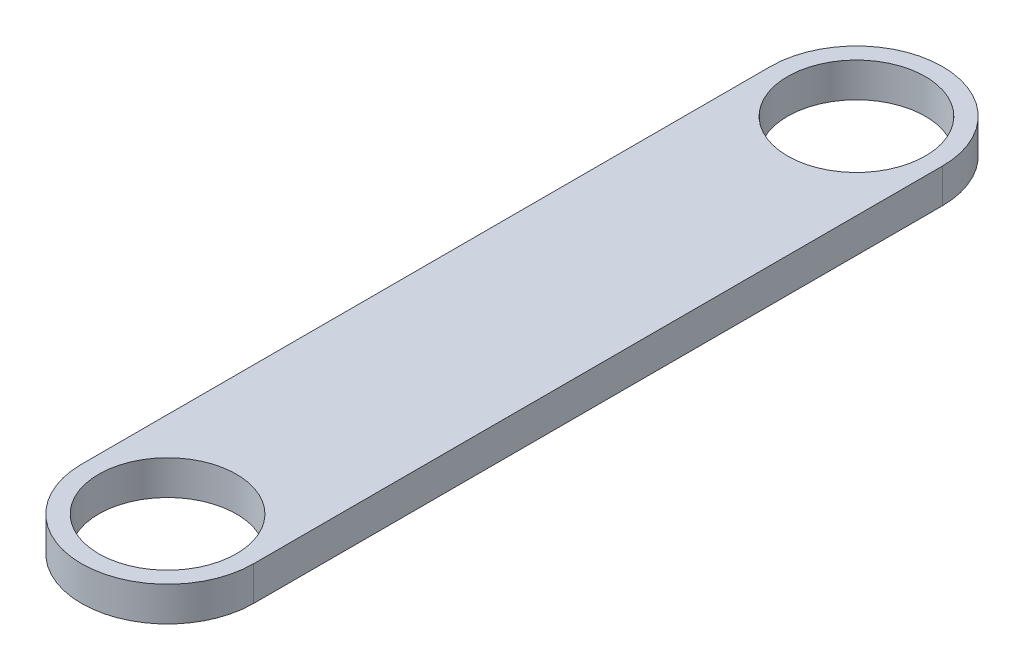
SolidWorks part; units mm, degrees
ref_plane "Front Plane" through (0, 0, 0) normal (0, 0, 1) x (1, 0, 0)
ref_plane "Top Plane" through (0, 0, 0) normal (0, 1, 0) x (1, 0, 0)
ref_plane "Right Plane" through (0, 0, 0) normal (1, 0, 0) x (0, 0, -1)
sketch "Sketch1" plane through (0, 0, 0) normal (0, 1, 0) x (1, 0, 0)
  line L0 (0, 0) -> (0, 20) construction
  line L1 (-2.5, 0) -> (-2.5, 20)
  line L2 (2.5, 0) -> (2.5, 20)
  arc A0 (-2.5, 0) -> (2.5, 0) centre (0, 0) ccw
  arc A1 (2.5, 20) -> (-2.5, 20) centre (0, 20) ccw
  circle A2 centre (0, 0) radius 2
  circle A3 centre (0, 20) radius 2
  point P3 (0, 10)
  dimension "D2" = 4
  dimension "D3" = 4
  dimension "D1" = 20
  dimension "D4" = 5
extrude "Boss-Extrude1" add sketch "Sketch1" along normal blind 1
